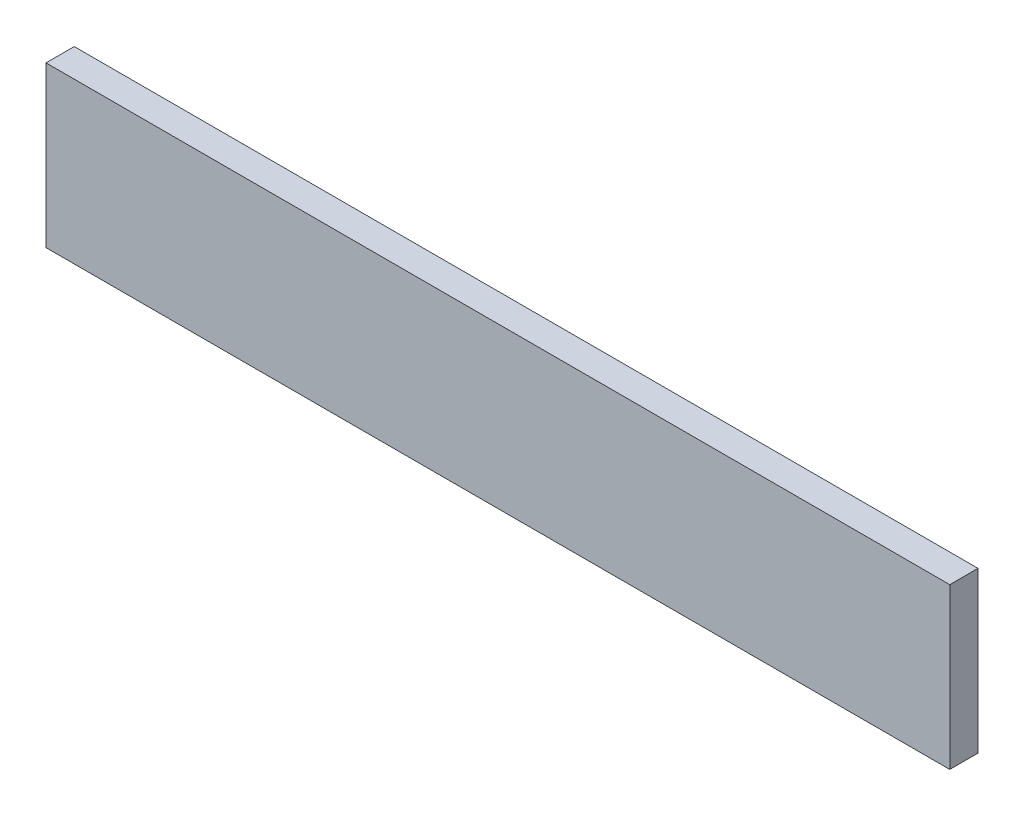
SolidWorks part; units mm, degrees
ref_plane "Front Plane" through (0, 0, 0) normal (0, 0, 1) x (1, 0, 0)
ref_plane "Top Plane" through (0, 0, 0) normal (0, 1, 0) x (1, 0, 0)
ref_plane "Right Plane" through (0, 0, 0) normal (1, 0, 0) x (0, 0, -1)
sketch "Sketch1" plane through (0, 0, 0) normal (0, 0, 1) x (1, 0, 0)
  line L1 (0, 107.95) -> (609.6, 107.95)
  line L2 (0, 107.95) -> (0, 0)
  line L3 (0, 0) -> (609.6, 0)
  line L4 (609.6, 107.95) -> (609.6, 0)
  dimension "D1" = 609.6
  dimension "D2" = 107.95
extrude "Boss-Extrude1" add sketch "Sketch1" along normal blind 19.05
